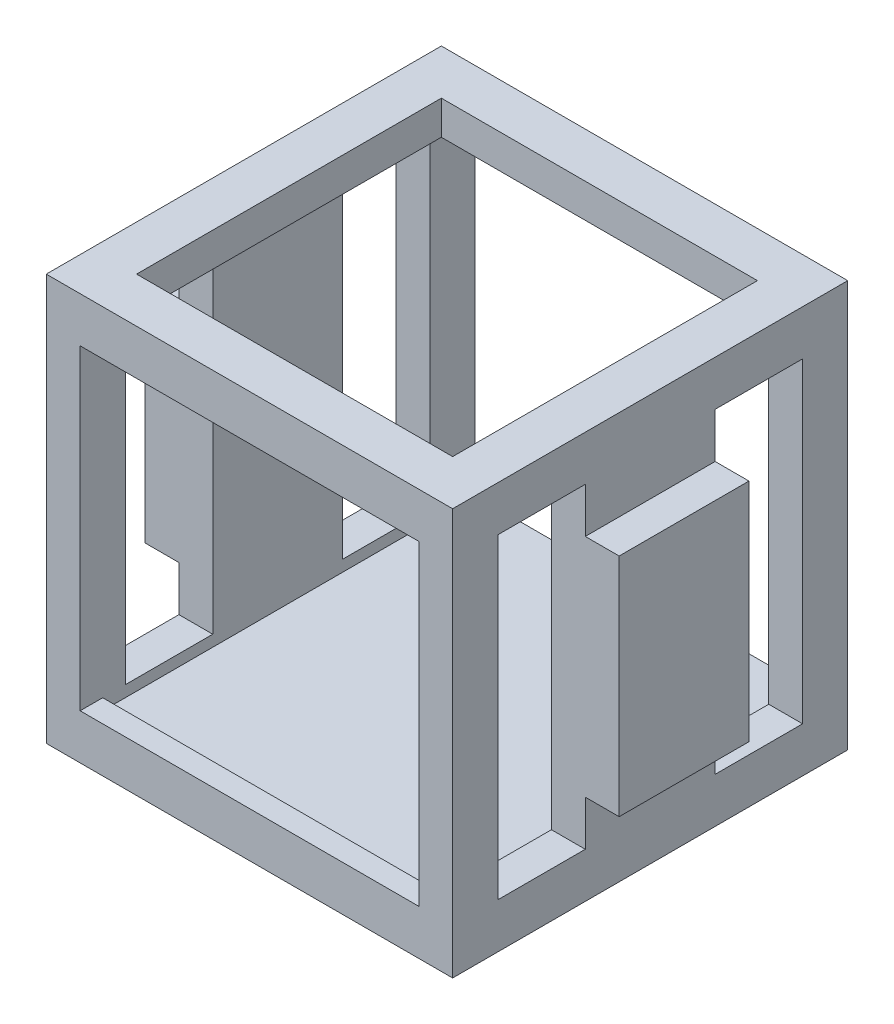
SolidWorks part; units mm, degrees
ref_plane "Front Plane" through (0, 0, 0) normal (0, 0, 1) x (1, 0, 0)
ref_plane "Top Plane" through (0, 0, 0) normal (0, 1, 0) x (1, 0, 0)
ref_plane "Right Plane" through (0, 0, 0) normal (1, 0, 0) x (0, 0, -1)
sketch "Sketch1" plane through (0, 0, 0) normal (0, 0, 1) x (1, 0, 0)
  line L1 (-18, 18) -> (18, 18)
  line L2 (-18, 18) -> (-18, -18)
  line L3 (-18, -18) -> (18, -18)
  line L4 (18, 18) -> (18, -18)
  line L5 (-18, 18) -> (18, -18) construction
  line L6 (-18, -18) -> (18, 18) construction
  point P0 (0, 0)
  dimension "D1" = 36
extrude "Boss-Extrude1" add sketch "Sketch1" along normal mid plane 35
sketch "Sketch2" plane through (0, 0, 0) normal (0, 0, 1) x (1, 0, 0)
  line L0 (18, -18) -> (18, 18) construction
  line L1 (-15, 15) -> (15, 15)
  line L2 (-15, 15) -> (-15, -15)
  line L3 (-15, -15) -> (15, -15)
  line L4 (15, 15) -> (15, -15)
  line L5 (-15, 15) -> (15, -15) construction
  line L6 (-15, -15) -> (15, 15) construction
  point P0 (0, 0)
  dimension "D1" = 3
extrude "Cut-Extrude1" cut sketch "Sketch2" against normal through all and the other way offset from surface (15.5 mm away) 2 other way up to face at (0, 0, 17.5)
sketch "Sketch3" plane through (0, 0, 17.5) normal (0, 0, 1) x (1, 0, 0)
  line L1 (-15, 14) -> (15, 14)
  line L2 (-15, 14) -> (-15, -14)
  line L3 (-15, -14) -> (15, -14)
  line L4 (15, 14) -> (15, -14)
  line L5 (-15, 14) -> (15, -14) construction
  line L6 (-15, -14) -> (15, 14) construction
  line L7 (18, 18) -> (-18, 18) construction
  line L8 (18, -18) -> (18, 18) construction
  point P0 (0, 0)
  dimension "D1" = 3
  dimension "D2" = 4
extrude "Cut-Extrude3" cut sketch "Sketch3" against normal through all
sketch "Sketch5" plane through (0, -18, 0) normal (0, -1, 0) x (-1, 0, 0)
  line L1 (-10, -10) -> (10, -10)
  line L2 (-10, -10) -> (-10, 10)
  line L3 (-10, 10) -> (10, 10)
  line L4 (10, -10) -> (10, 10)
  line L5 (-10, -10) -> (10, 10) construction
  line L6 (-10, 10) -> (10, -10) construction
  point P0 (0, 0)
  dimension "D1" = 20
  dimension "D2" = 20
extrude "Boss-Extrude2" add sketch "Sketch5" along normal blind 7
sketch "Sketch6" plane through (10, 0, 0) normal (1, 0, 0) x (0, 0, -1)
  line L0 (-5.3, -18.5) -> (5.3, -18.5)
  line L1 (-17.5, -18) -> (17.5, -18) construction
  arc A0 (-5.3, -18.5) -> (5.3, -18.5) centre (0, -18.5) ccw
  point P6 (0, 0)
  dimension "D1" = 5.3
  dimension "D2" = 0.5
extrude "Cut-Extrude4" cut sketch "Sketch6" against normal through all
sketch "Sketch7" plane through (18, 0, 0) normal (1, 0, 0) x (0, 0, -1)
  line L1 (-5.75, -10) -> (5.75, -10)
  line L2 (-5.75, -10) -> (-5.75, 10)
  line L3 (-5.75, 10) -> (5.75, 10)
  line L4 (5.75, -10) -> (5.75, 10)
  line L5 (-5.75, -10) -> (5.75, 10) construction
  line L6 (-5.75, 10) -> (5.75, -10) construction
  point P0 (0, 0)
  point P6 (0, 10)
  dimension "D1" = 11.5
  dimension "D2" = 20
extrude "Boss-Extrude3" add sketch "Sketch7" along normal blind 3
ref_plane "Plane1" through (0, 0, 0) normal (-1, 0, 0) x (0, 0, 1)
mirror "Mirror1" about plane through (0, 0, 0) normal (1, 0, 0) of "Boss-Extrude3"
ref_plane "Plane2" through (10, -18, 10) normal (0, 1, 0) x (1, 0, 0)
sketch "Sketch9" plane through (10, 0, 0) normal (1, 0, 0) x (0, 0, -1)
  line L0 (-8.3, -18.5) -> (8.7093, -18.5) construction
  line L1 (5.3, -18.5) -> (-5.3, -18.5) construction
  line L4 (-8.3, -18.5) -> (-10, -18.5)
  line L5 (-10, -25) -> (-10, -18) construction
  line L6 (-10, -18.5) -> (-10, -28.666)
  line L7 (8.7093, -18.5) -> (10, -18.5)
  line L8 (10, -25) -> (10, -18) construction
  line L9 (10, -18.5) -> (10, -28.666)
  line L10 (10, -28.666) -> (-10, -28.666)
  arc A0 (-8.3, -18.5) -> (8.7093, -18.5) centre (0.2047, -18.5) ccw
  dimension "D1" = 3
extrude "Cut-Extrude5" cut sketch "Sketch9" against normal through all
sketch "Sketch10" plane through (0, 18, 0) normal (0, 1, 0) x (1, 0, 0)
  line L0 (18, 17.5) -> (-18, 17.5) construction
  line L1 (-14, -13.5) -> (14, -13.5)
  line L2 (-14, -13.5) -> (-14, 13.5)
  line L3 (-14, 13.5) -> (14, 13.5)
  line L4 (14, -13.5) -> (14, 13.5)
  line L5 (-14, -13.5) -> (14, 13.5) construction
  line L6 (-14, 13.5) -> (14, -13.5) construction
  line L7 (-18, -17.5) -> (-18, 17.5) construction
  point P0 (0, 0)
  dimension "D1" = 4
  dimension "D2" = 4
extrude "Cut-Extrude6" cut sketch "Sketch10" against normal up to next
sketch "Sketch11" plane through (18, 0, 0) normal (1, 0, 0) x (0, 0, -1)
  line L0 (-17.5, -18) -> (-17.5, 18) construction
  line L1 (-5.75, -14) -> (-13.5, -14)
  line L2 (-5.75, -14) -> (-5.75, 14)
  line L3 (-5.75, 14) -> (-13.5, 14)
  line L4 (-13.5, -14) -> (-13.5, 14)
  line L5 (5.75, 14) -> (13.5, 14)
  line L6 (5.75, 14) -> (5.75, -14)
  line L7 (5.75, -14) -> (13.5, -14)
  line L8 (13.5, 14) -> (13.5, -14)
  line L9 (17.5, -18) -> (17.5, 18) construction
  line L10 (-17.5, 18) -> (17.5, 18) construction
  line L11 (-17.5, -18) -> (17.5, -18) construction
  line L13 (-5.75, 10) -> (-5.75, -10) construction
  line L14 (5.75, -10) -> (5.75, 10) construction
  dimension "D1" = 4
  dimension "D2" = 4
  dimension "D3" = 4
  dimension "D4" = 4
  dimension "D5" = 4
  dimension "D6" = 4
extrude "Cut-Extrude7" cut sketch "Sketch11" against normal through all
